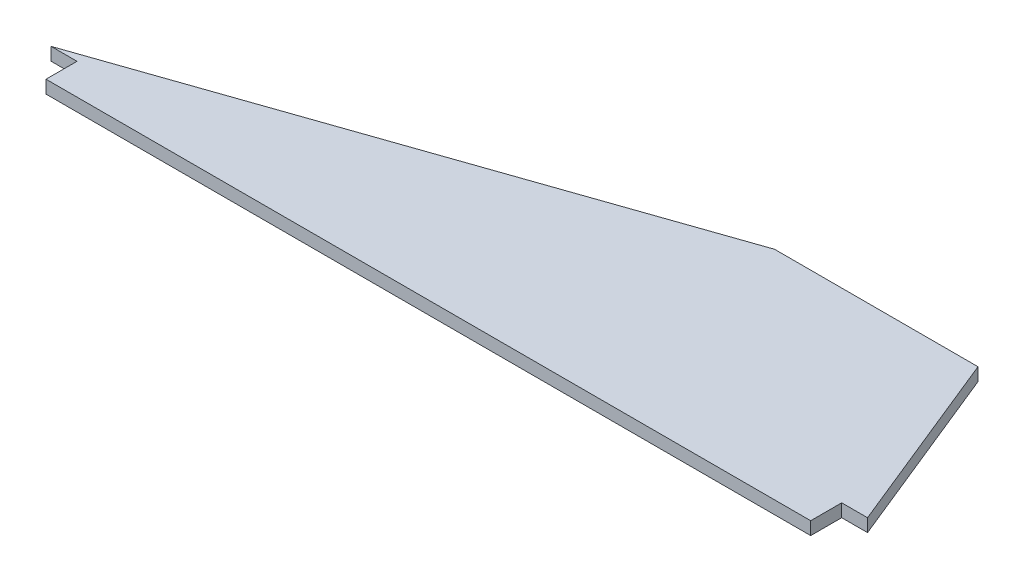
SolidWorks part; units mm, degrees
ref_plane "Front Plane" through (0, 0, 0) normal (0, 0, 1) x (1, 0, 0)
ref_plane "Top Plane" through (0, 0, 0) normal (0, 1, 0) x (1, 0, 0)
ref_plane "Right Plane" through (0, 0, 0) normal (1, 0, 0) x (0, 0, -1)
sketch "Sketch1" plane through (0, 0, 0) normal (0, 1, 0) x (1, 0, 0)
  line L0 (0, 0) -> (132.08, 45.72)
  line L5 (132.08, 45.72) -> (182.0926, 45.72)
  line L6 (182.0926, 45.72) -> (200.66, 0)
  line L7 (0, 0) -> (6.35, 0)
  line L9 (6.35, 0) -> (6.35, -7.62)
  line L10 (6.35, -7.62) -> (194.31, -7.62)
  line L11 (194.31, 0) -> (194.31, -7.62)
  line L12 (194.31, 0) -> (200.66, 0)
  dimension "D1" = 132.08
  dimension "D2" = 182.0926
  dimension "D3" = 45.72
  dimension "D4" = 187.96
  dimension "D5" = 7.62
  dimension "D6" = 200.66
  dimension "D7" = 6.35
extrude "Boss-Extrude1" add sketch "Sketch1" along normal blind 3.175
ref_plane "midplane" through (0, 1.5875, 0) normal (0, 1, 0) x (1, 0, 0)
ref_plane "backplane" through (200.66, 0, 0) normal (1, 0, 0) x (0, 0, -1)
